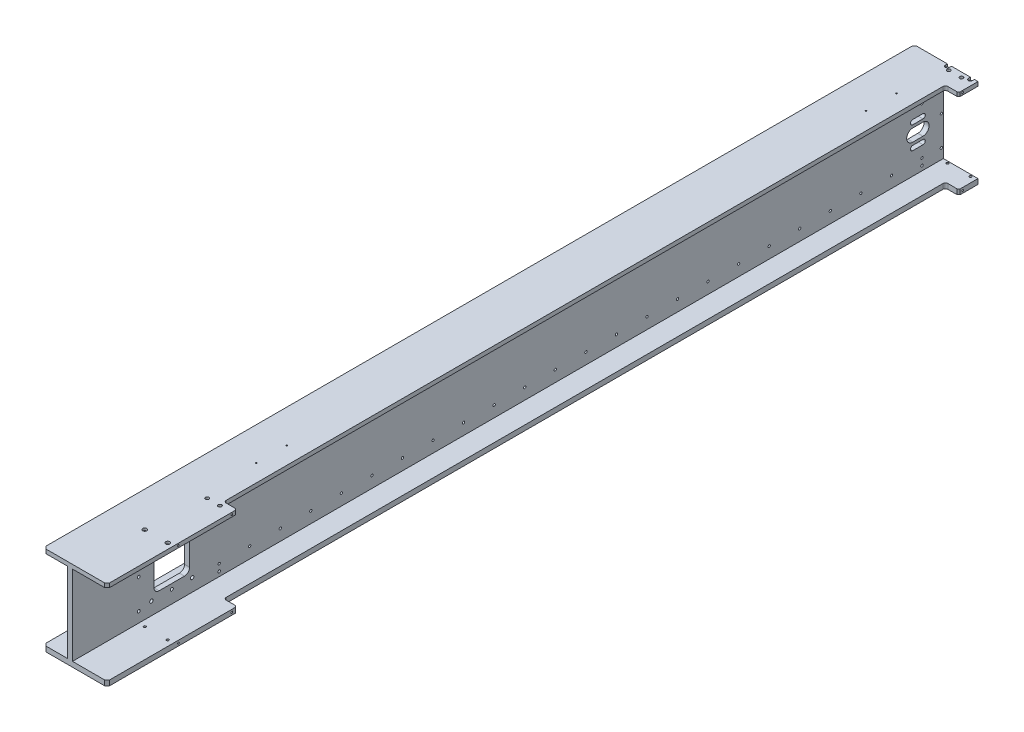
SolidWorks part; units mm, degrees
ref_plane "Front" through (0, 0, 0) normal (0, 0, 1) x (1, 0, 0)
ref_plane "Top" through (0, 0, 0) normal (0, 1, 0) x (1, 0, 0)
ref_plane "Right" through (0, 0, 0) normal (1, 0, 0) x (0, 0, -1)
sketch "Sketch1" plane through (0, 0, 0) normal (0, 1, 0) x (1, 0, 0)
  line L1 (-125, 0) -> (0, 0)
  line L2 (-125, 0) -> (-125, 1710)
  line L3 (-125, 1710) -> (0, 1710)
  line L4 (0, 0) -> (0, 1710)
  dimension "D1" = 1710
  dimension "D2" = 125
extrude "Boss-Extrude1" add sketch "Sketch1" against normal blind 8
sketch "Sketch2" plane through (0, 0, 0) normal (1, 0, 0) x (0, 0, -1)
  line L0 (0, -8) -> (0, 0) construction
  line L1 (0, -8) -> (1710, -8)
  line L2 (0, -8) -> (0, -165)
  line L3 (0, -165) -> (1710, -165)
  line L4 (1710, -8) -> (1710, -165)
  line L5 (0, -8) -> (1710, -8) construction
  line L6 (1710, -8) -> (1710, 0) construction
  dimension "D1" = 157
extrude "Boss-Extrude2" add sketch "Sketch2" against normal blind 10 from offset 68
sketch "Sketch3" plane through (0, -165, 0) normal (0, -1, 0) x (1, 0, 0)
  line L1 (-125, 0) -> (0, 0)
  line L2 (-125, 0) -> (-125, -1710)
  line L3 (-125, -1710) -> (0, -1710)
  line L4 (0, 0) -> (0, -1710)
extrude "Boss-Extrude3" add sketch "Sketch3" along normal blind 10
sketch "Sketch4" plane through (0, 0, 0) normal (0, 0, 1) x (1, 0, 0)
  line L0 (-78, -8) -> (-78, -165) construction
  line L1 (-125, -8) -> (-78, -8)
  line L2 (-125, -8) -> (-125, -165)
  line L3 (-125, -165) -> (-78, -165)
  line L4 (-78, -8) -> (-78, -165)
extrude "Boss-Extrude4" add sketch "Sketch4" against normal blind 8 from offset 50
sketch "Sketch5" plane through (0, 0, -50) normal (0, 0, 1) x (1, 0, 0)
  line L4 (-125, -8) -> (-125, -165)
  line L5 (-125, -165) -> (-78, -165)
  line L6 (-78, -165) -> (-78, -8)
  line L7 (-78, -8) -> (-125, -8)
  line L8 (-125, -8) -> (-125, -165)
  line L9 (-125, -165) -> (-78, -165)
  line L10 (-78, -165) -> (-78, -8)
  line L11 (-78, -8) -> (-125, -8)
  dimension "D1" = 0
extrude "Boss-Extrude5" add sketch "Sketch5" against normal blind 8 from offset 500 offset against normal yes
sketch "Sketch6" plane through (0, 0, -550) normal (0, 0, 1) x (1, 0, 0)
  line L4 (-78, -8) -> (-125, -8)
  line L5 (-125, -8) -> (-125, -165)
  line L6 (-125, -165) -> (-78, -165)
  line L7 (-78, -165) -> (-78, -8)
  line L8 (-78, -8) -> (-125, -8)
  line L9 (-125, -8) -> (-125, -165)
  line L10 (-125, -165) -> (-78, -165)
  line L11 (-78, -165) -> (-78, -8)
  dimension "D1" = 0
extrude "Boss-Extrude6" add sketch "Sketch6" against normal blind 8 from offset 490 offset against normal yes
sketch "Sketch7" plane through (0, 0, -1040) normal (0, 0, 1) x (1, 0, 0)
  line L4 (-78, -165) -> (-78, -8)
  line L5 (-78, -8) -> (-125, -8)
  line L6 (-125, -8) -> (-125, -165)
  line L7 (-125, -165) -> (-78, -165)
  line L8 (-78, -165) -> (-78, -8)
  line L9 (-78, -8) -> (-125, -8)
  line L10 (-125, -8) -> (-125, -165)
  line L11 (-125, -165) -> (-78, -165)
  dimension "D1" = 0
extrude "Boss-Extrude7" add sketch "Sketch7" against normal blind 8 from offset 530 offset against normal yes
sketch "Sketch8" plane through (0, 0, 0) normal (0, 1, 0) x (1, 0, 0)
  line L0 (0, 0) -> (0, 1710) construction
  line L1 (0, 255) -> (-26, 255)
  line L2 (0, 255) -> (0, 1672)
  line L3 (0, 1672) -> (-26, 1672)
  line L4 (-26, 255) -> (-26, 1672)
  dimension "D1" = 255
  dimension "D2" = 1417
  dimension "D3" = 26
extrude "Cut-Extrude1" cut sketch "Sketch8" against normal through all
sketch "Sketch9" plane through (0, 0, 0) normal (0, 1, 0) x (1, 0, 0)
  line L0 (-56, 1706) -> (-56, 1710) construction
  line L1 (-60, 1706) -> (-60, 1710)
  line L2 (-52, 1706) -> (-52, 1710)
  line L3 (-11, 1706) -> (-11, 1710) construction
  line L4 (-15, 1706) -> (-15, 1710)
  line L5 (-7, 1706) -> (-7, 1710)
  line L7 (-7, 1710) -> (-15, 1710)
  line L8 (0, 1710) -> (-125, 1710) construction
  line L9 (-52, 1710) -> (-60, 1710)
  line L10 (0, 1672) -> (0, 1710) construction
  arc A0 (-60, 1706) -> (-52, 1706) centre (-56, 1706) ccw
  arc A2 (-15, 1706) -> (-7, 1706) centre (-11, 1706) ccw
  dimension "D4" = 8
  dimension "D1" = 1706
  dimension "D2" = 11
  dimension "D3" = 45
extrude "Cut-Extrude2" cut sketch "Sketch9" against normal blind 4.5
sketch "Sketch10" plane through (0, -175, 0) normal (0, -1, 0) x (1, 0, 0)
  line L0 (-60, -1710) -> (-60, -1706) construction
  line L1 (-52, -1706) -> (-52, -1710) construction
  line L2 (-52, -1710) -> (-60, -1710) construction
  line L3 (-15, -1710) -> (-15, -1706) construction
  line L4 (-7, -1706) -> (-7, -1710) construction
  line L5 (-7, -1710) -> (-15, -1710) construction
  line L6 (-60, -1710) -> (-60, -1706)
  line L7 (-52, -1706) -> (-52, -1710)
  line L8 (-52, -1710) -> (-60, -1710)
  line L9 (-15, -1710) -> (-15, -1706)
  line L10 (-7, -1706) -> (-7, -1710)
  line L11 (-7, -1710) -> (-15, -1710)
  arc A0 (-52, -1706) -> (-60, -1706) centre (-56, -1706) ccw construction
  arc A1 (-7, -1706) -> (-15, -1706) centre (-11, -1706) ccw construction
  arc A2 (-52, -1706) -> (-60, -1706) centre (-56, -1706) ccw
  arc A3 (-7, -1706) -> (-15, -1706) centre (-11, -1706) ccw
extrude "Cut-Extrude3" cut sketch "Sketch10" against normal blind 4.5
sketch "Sketch11" plane through (-68, 0, 0) normal (1, 0, 0) x (0, 0, -1)
  line L1 (160, -60) -> (230, -60)
  line L2 (160, -60) -> (160, -130)
  line L3 (160, -130) -> (230, -130)
  line L4 (230, -60) -> (230, -130)
  dimension "D1" = 160
  dimension "D2" = 70
  dimension "D3" = 60
  dimension "D4" = 70
extrude "Cut-Extrude4" cut sketch "Sketch11" against normal up to next
sketch "Sketch12" plane through (-68, 0, 0) normal (1, 0, 0) x (0, 0, -1)
  circle A0 centre (288, -156) radius 2.5
  circle A1 centre (1668, -156) radius 2.5
  circle A3 centre (1668, -50) radius 2.5
  circle A5 centre (288, -50) radius 2.5
  dimension "D1" = 5
  dimension "D2" = 288
  dimension "D3" = 1380
  dimension "D4" = 50
  dimension "D5" = 106
extrude "Cut-Extrude5" cut sketch "Sketch12" against normal up to next
sketch "Sketch29" plane through (-68, 0, 0) normal (1, 0, 0) x (0, 0, -1)
  line L0 (1650, -95) -> (1670, -95) construction
  line L1 (1650, -83) -> (1670, -83)
  line L2 (1650, -107) -> (1670, -107)
  line L3 (1672, 0) -> (1710, 0) construction
  line L7 (1629.6521, -95) -> (1689.2505, -95) construction
  arc A0 (1650, -83) -> (1650, -107) centre (1650, -95) ccw
  arc A1 (1670, -107) -> (1670, -83) centre (1670, -95) ccw
  point P2 (1660, -95)
  dimension "D4" = 24
  dimension "D1" = 1660
  dimension "D2" = 20
  dimension "D3" = 95
extrude "Cut-Extrude6" cut sketch "Sketch29" against normal up to next
sketch "Sketch30" plane through (-68, 0, 0) normal (1, 0, 0) x (0, 0, -1)
  line L0 (1631.9328, -95) -> (1687.8244, -95) construction
  line L1 (1670, -83) -> (1650, -83) construction
  line L2 (1650, -107) -> (1670, -107) construction
  line L3 (1650, -73) -> (1670, -73) construction
  line L4 (1650, -68.5) -> (1670, -68.5)
  line L5 (1650, -77.5) -> (1670, -77.5)
  line L6 (1650, -117) -> (1670, -117) construction
  line L7 (1650, -121.5) -> (1670, -121.5)
  line L8 (1650, -112.5) -> (1670, -112.5)
  arc A0 (1650, -68.5) -> (1650, -77.5) centre (1650, -73) ccw
  arc A1 (1670, -77.5) -> (1670, -68.5) centre (1670, -73) ccw
  arc A2 (1650, -121.5) -> (1650, -112.5) centre (1650, -117) cw
  arc A3 (1670, -112.5) -> (1670, -121.5) centre (1670, -117) cw
  arc A4 (1650, -83) -> (1650, -107) centre (1650, -95) ccw construction
  arc A5 (1650, -83) -> (1650, -107) centre (1650, -95) ccw construction
  arc A6 (1670, -107) -> (1670, -83) centre (1670, -95) ccw construction
  arc A7 (1670, -107) -> (1670, -83) centre (1670, -95) ccw construction
  point P8 (1660, -73)
  point P15 (1660, -117)
  dimension "D2" = 9
  dimension "D1" = 20
  dimension "D3" = 44
extrude "Cut-Extrude7" cut sketch "Sketch30" against normal up to next
sketch "Sketch37" plane through (-68, 0, 0) normal (1, 0, 0) x (0, 0, -1)
  circle A0 centre (195, -50) radius 3
  circle A1 centre (195, -140) radius 3
  dimension "D1" = 6
  dimension "D2" = 6
  dimension "D3" = 195
  dimension "D4" = 50
  dimension "D5" = 90
extrude "Cut-Extrude8" cut sketch "Sketch37" against normal up to next
sketch "Sketch40" plane through (0, 0, -50) normal (0, 0, 1) x (1, 0, 0)
  line L0 (-78, -8) -> (-83, -8)
  line L1 (-78, -8) -> (-125, -8) construction
  line L2 (-83, -8) -> (-78, -13)
  line L3 (-78, -165) -> (-78, -8) construction
  line L4 (-78, -13) -> (-78, -8)
  line L5 (-78, -165) -> (-78, -160)
  line L6 (-78, -160) -> (-83, -165)
  line L7 (-125, -165) -> (-78, -165) construction
  line L8 (-83, -165) -> (-78, -165)
  dimension "D1" = 5
extrude "Cut-Extrude9" cut sketch "Sketch40" against normal through all
hole_wizard "CBORE for M4 Socket Head Cap Screw3" positions "Sketch14" profile "Sketch13" counterbore size "M4" standard "JIS" end condition up to next
sketch "Sketch14" plane through (0, 0, 0) normal (0, 1, 0) x (-1, 0, 0)
  point P0 (56, -130)
  point P1 (11, -130)
  dimension "D1" = 45
  dimension "D2" = 11
  dimension "D3" = 130
sketch "Sketch13" plane through (-56, 0, -130) normal (1, 0, 0) x (0, 0, 1)
  line L0 (0, 0) -> (0, 8)
  line L1 (0, 8) -> (2.25, 8)
  line L3 (2.25, 8) -> (2.25, 4.5)
  line L4 (2.25, 4.5) -> (4, 4.5)
  line L5 (4, 4.5) -> (4, 0)
  line L7 (4, 0) -> (0, 0)
  line L11 (0, -6.35) -> (0, 107.95) construction
  dimension "Thru Hole Dia." = 4.5
  dimension "Thru Hole Depth" = 8
  dimension "C'Bore Dia." = 8
  dimension "C'Bore Depth" = 4.5
hole_wizard "CBORE for M4 Socket Head Cap Screw2" positions "Sketch18" profile "Sketch17" counterbore size "M4" standard "JIS" end condition up to next
sketch "Sketch18" plane through (0, -175, 0) normal (0, -1, 0) x (1, 0, 0)
  point P0 (-56, -130)
  point P1 (-11, -130)
sketch "Sketch17" plane through (-56, -175, -130) normal (1, 0, 0) x (0, 0, -1)
  line L0 (0, 0) -> (0, 10)
  line L1 (0, 10) -> (2.25, 10)
  line L3 (2.25, 10) -> (2.25, 4.5)
  line L4 (2.25, 4.5) -> (4, 4.5)
  line L5 (4, 4.5) -> (4, 0)
  line L7 (4, 0) -> (0, 0)
  line L11 (0, -6.35) -> (0, 107.95) construction
  dimension "Thru Hole Dia." = 4.5
  dimension "Thru Hole Depth" = 10
  dimension "C'Bore Dia." = 8
  dimension "C'Bore Depth" = 4.5
hole_wizard "M8x1.25 Tapped Hole1" positions "Sketch16" profile "Sketch15" tap size "M8x1.25" standard "JIS" end condition up to next
sketch "Sketch16" plane through (0, 0, 0) normal (0, 1, 0) x (-1, 0, 0)
  line L0 (0, 0) -> (0, -255) construction
  point P0 (48, -244.5)
  point P1 (23, -244.5)
  point P7 (48, -1700.5)
  point P9 (23, -1700.5)
  dimension "D1" = 244.5
  dimension "D2" = 23
  dimension "D3" = 25
  dimension "D4" = 1456
sketch "Sketch15" plane through (-48, 0, -244.5) normal (1, 0, 0) x (0, 0, 1)
  line L0 (0, 0) -> (0, 8)
  line L1 (0, 8) -> (3.4, 8)
  line L2 (3.4, 8) -> (3.4, 0)
  line L5 (3.4, 0) -> (0, 0)
  line L11 (0, -6.35) -> (0, 107.95) construction
  dimension "Thru Tap Drill Dia." = 6.8
  dimension "Thru Tap Drill Depth" = 8
cosmetic thread "Hole Thread1" parameters "D2"=8
cosmetic thread "Hole Thread2" parameters "D2"=8
cosmetic thread "Hole Thread3" parameters "D2"=8
cosmetic thread "Hole Thread4" parameters "D2"=8
hole_wizard "Ø5.5 (5.5) Diameter Hole1" positions "Sketch36" profile "Sketch35" hole size "Ø5.5" standard "JIS" end condition up to next
sketch "Sketch36" plane through (-78, 0, 0) normal (-1, 0, 0) x (0, 0, 1)
  point P0 (-130, -28)
  point P1 (-130, -86.5)
  point P3 (-130, -145)
  dimension "D1" = 58.5
  dimension "D2" = 58.5
  dimension "D3" = 130
  dimension "D4" = 28
sketch "Sketch35" plane through (-78, -28, -130) normal (0, 1, 0) x (0, 0, 1)
  line L0 (0, 0) -> (0, 10)
  line L1 (0, 10) -> (2.75, 10)
  line L2 (2.75, 10) -> (2.75, 0)
  line L5 (2.75, 0) -> (0, 0)
  line L11 (0, -6.35) -> (0, 107.95) construction
  dimension "Thru Hole Dia." = 5.5
  dimension "Thru Hole Depth" = 10
hole_wizard "M8x1.25 Tapped Hole3" positions "Sketch25" profile "Sketch24" tap size "M8x1.25" standard "JIS" end condition up to next
sketch "Sketch25" plane through (-78, 0, 0) normal (-1, 0, 0) x (0, 0, 1)
  point P0 (-155, -50)
  point P1 (-235, -50)
  point P3 (-235, -140)
  point P5 (-155, -140)
  dimension "D1" = 155
  dimension "D2" = 80
  dimension "D3" = 50
  dimension "D4" = 90
sketch "Sketch24" plane through (-78, -50, -155) normal (0, 1, 0) x (0, 0, 1)
  line L0 (0, 0) -> (0, 10)
  line L1 (0, 10) -> (3.4, 10)
  line L2 (3.4, 10) -> (3.4, 0)
  line L5 (3.4, 0) -> (0, 0)
  line L11 (0, -6.35) -> (0, 107.95) construction
  dimension "Thru Tap Drill Dia." = 6.8
  dimension "Thru Tap Drill Depth" = 10
cosmetic thread "Hole Thread9" parameters "D2"=8
cosmetic thread "Hole Thread10" parameters "D2"=8
cosmetic thread "Hole Thread11" parameters "D2"=8
cosmetic thread "Hole Thread12" parameters "D2"=8
hole_wizard "Ø4.5 (4.5) Diameter Hole1" positions "Sketch28" profile "Sketch27" hole size "Ø4.5" standard "JIS" end condition up to next
sketch "Sketch28" plane through (-68, 0, 0) normal (1, 0, 0) x (0, 0, -1)
  point P0 (288, -37)
  dimension "D1" = 288
  dimension "D2" = 37
sketch "Sketch27" plane through (-68, -37, -288) normal (0, 1, 0) x (0, 0, -1)
  line L0 (0, 0) -> (0, 10.001)
  line L1 (0, 10.001) -> (2.25, 10.001)
  line L2 (2.25, 10.001) -> (2.25, 0)
  line L5 (2.25, 0) -> (0, 0)
  line L11 (0, -6.35) -> (0, 107.95) construction
  dimension "Thru Hole Dia." = 4.5
  dimension "Thru Hole Depth" = 10.001
hole_wizard "Ø4.5 (4.5) Diameter Hole2" positions "Sketch23" profile "Sketch22" hole size "Ø4.5" standard "JIS" end condition up to next
sketch "Sketch23" plane through (-78, 0, 0) normal (-1, 0, 0) x (0, 0, 1)
  line L0 (-1672, 0) -> (-1710, 0) construction
  point P13 (-1706, -28)
  point P15 (-1706, -86.5)
  point P17 (-1706, -145)
  dimension "D5" = 1706
  dimension "D6" = 28
  dimension "D7" = 58.5
  dimension "D8" = 58.5
sketch "Sketch22" plane through (-78, -28, -1706) normal (0, 1, 0) x (0, 0, 1)
  line L0 (0, 0) -> (0, 10)
  line L1 (0, 10) -> (2.25, 10)
  line L2 (2.25, 10) -> (2.25, 0)
  line L5 (2.25, 0) -> (0, 0)
  line L11 (0, -6.35) -> (0, 107.95) construction
  dimension "Thru Hole Dia." = 4.5
  dimension "Thru Hole Depth" = 10
hole_wizard "Ø4.5 (4.5) Diameter Hole3" positions "Sketch42" profile "Sketch43" hole size "Ø4.5" standard "JIS" end condition up to next
sketch "Sketch42" plane through (0, -4.5, 0) normal (0, 1, 0) x (-1, 0, 0)
  point P0 (56, -1706)
  point P1 (11, -1706)
sketch "Sketch43" plane through (-56, -4.5, -1706) normal (1, 0, 0) x (0, 0, 1)
  line L0 (0, 0) -> (0, 3.5)
  line L1 (0, 3.5) -> (2.25, 3.5)
  line L2 (2.25, 3.5) -> (2.25, 0)
  line L5 (2.25, 0) -> (0, 0)
  line L11 (0, -6.35) -> (0, 107.95) construction
  dimension "Thru Hole Dia." = 4.5
  dimension "Thru Hole Depth" = 3.5
hole_wizard "Ø4.5 (4.5) Diameter Hole4" positions "Sketch45" profile "Sketch46" hole size "Ø4.5" standard "JIS" end condition up to next
sketch "Sketch45" plane through (0, -170.5, 0) normal (0, -1, 0) x (1, 0, 0)
  point P0 (-11, -1706)
  point P1 (-56, -1706)
sketch "Sketch46" plane through (-11, -170.5, -1706) normal (1, 0, 0) x (0, 0, -1)
  line L0 (0, 0) -> (0, 5.5)
  line L1 (0, 5.5) -> (2.25, 5.5)
  line L2 (2.25, 5.5) -> (2.25, 0)
  line L5 (2.25, 0) -> (0, 0)
  line L11 (0, -6.35) -> (0, 107.95) construction
  dimension "Thru Hole Dia." = 4.5
  dimension "Thru Hole Depth" = 5.5
pattern_linear "LPattern1" count 2 spacing 106 along (0, -1, 0) count 24 spacing 60 along (0, 0, -1) of "Ø4.5 (4.5) Diameter Hole1"
hole_wizard "M4x0.7 Tapped Hole1" positions "Sketch32" profile "Sketch31" tap size "M4x0.7" standard "JIS"
sketch "Sketch32" plane through (0, 0, 0) normal (1, 0, 0) x (0, 0, -1)
  point P0 (140, -4)
  point P14 (245, -4)
  point P16 (1680, -4)
  dimension "D1" = 4
  dimension "D2" = 1435
  dimension "D3" = 140
  dimension "D4" = 105
sketch "Sketch31" plane through (0, -4, -140) normal (0, 1, 0) x (0, 0, -1)
  line L0 (0, 0) -> (0, 11.0914)
  line L1 (0, 11.0914) -> (1.65, 10.1)
  line L2 (1.65, 10.1) -> (1.65, 0)
  line L5 (1.65, 0) -> (0, 0)
  line L10 (0, 11.0914) -> (-1.65, 10.1) construction
  line L11 (0, -6.35) -> (0, 107.95) construction
  dimension "Tap Drill Dia." = 3.3
  dimension "Tap Drill Depth" = 10.1
  dimension "Drill Angle" = 118
cosmetic thread "Hole Thread13" parameters "D1"=8, "D2"=4
cosmetic thread "Hole Thread17" parameters "D1"=8, "D2"=4
cosmetic thread "Hole Thread18" parameters "D1"=8, "D2"=4
hole_wizard "M3x0.5 Tapped Hole1" positions "Sketch39" profile "Sketch38" tap size "M3x0.5" standard "JIS" end condition up to next
sketch "Sketch39" plane through (0, 0, 0) normal (0, 1, 0) x (-1, 0, 0)
  line L0 (125, 0) -> (0, 0) construction
  line L1 (0, 0) -> (0, -255) construction
  point P0 (60, -352.5)
  point P1 (60, -412.5)
  dimension "D1" = 352.5
  dimension "D2" = 60
  dimension "D3" = 60
sketch "Sketch38" plane through (-60, 0, -352.5) normal (1, 0, 0) x (0, 0, 1)
  line L0 (0, 0) -> (0, 8)
  line L1 (0, 8) -> (1.25, 8)
  line L2 (1.25, 8) -> (1.25, 0)
  line L5 (1.25, 0) -> (0, 0)
  line L11 (0, -6.35) -> (0, 107.95) construction
  dimension "Thru Tap Drill Dia." = 2.5
  dimension "Thru Tap Drill Depth" = 8
cosmetic thread "Hole Thread19" parameters "D2"=3
cosmetic thread "Hole Thread20" parameters "D2"=3
pattern_linear "LPattern3" count 2 spacing 1197.5 along (0, 0, -1) of "M3x0.5 Tapped Hole1"
pattern_linear "LPattern2" count 2 spacing 166 along (0, -1, 0) of "M4x0.7 Tapped Hole1"
fillet "Fillet1" radius 10 4 edges at (-73, -130, -160) (-73, -130, -230) (-73, -60, -230) (-73, -60, -160)
fillet "Fillet2" radius 5 4 edges at (-26, -170, -255) (-26, -170, -1672) (-26, -4, -1672) (-26, -4, -255)
chamfer "Chamfer1" distance 3 angle 45 4 edges at (0, -170, -1672) (0, -4, -1672) (0, -4, -255) (0, -170, -255)
chamfer "Chamfer2" distance 5 angle 45 6 edges at (-125, -170, -1710) (-125, -4, -1710) (-125, -170, 0) (-125, -4, 0) (0, -170, 0) (0, -4, 0)
